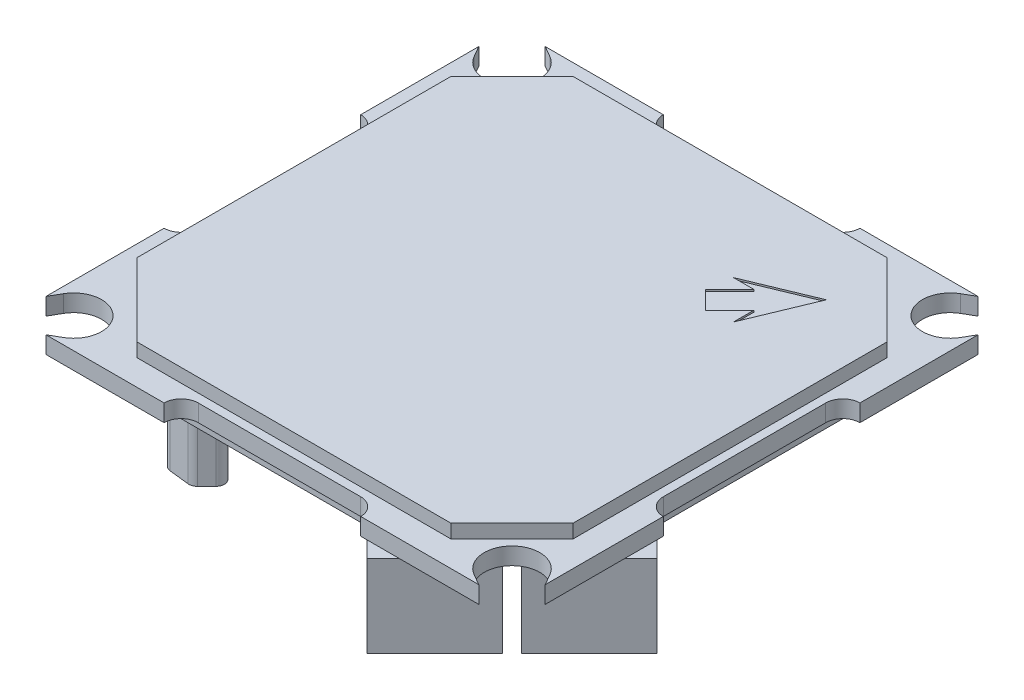
SolidWorks part; units mm, degrees
ref_plane "Front Plane" through (0, 0, 0) normal (0, 0, 1) x (1, 0, 0)
ref_plane "Top Plane" through (0, 0, 0) normal (0, 1, 0) x (1, 0, 0)
ref_plane "Right Plane" through (0, 0, 0) normal (1, 0, 0) x (0, 0, -1)
sketch "Sketch1" plane through (0, 0, 0) normal (0, 1, 0) x (1, 0, 0)
  line L1 (-14.6, -14.6) -> (14.6, -14.6)
  line L2 (-14.6, -14.6) -> (-14.6, 14.6)
  line L3 (-14.6, 14.6) -> (14.6, 14.6)
  line L4 (14.6, -14.6) -> (14.6, 14.6)
  line L5 (-14.6, -14.6) -> (14.6, 14.6) construction
  line L6 (-14.6, 14.6) -> (14.6, -14.6) construction
  point P0 (0, 0)
  dimension "D1" = 29.2
extrude "Boss-Extrude1" add sketch "Sketch1" along normal mid plane 1
sketch "Sketch2" plane through (0, 0.5, 0) normal (0, 1, 0) x (1, 0, 0)
  line L0 (-14.6, 4.75) -> (-14.6, -4.75) construction
  line L1 (-14.6, 14.6) -> (-14.6, -14.6) construction
  line L2 (-13.6, 4.75) -> (-13.6, -4.75)
  line L3 (-15.6, 4.75) -> (-15.6, -4.75)
  arc A0 (-13.6, 4.75) -> (-15.6, 4.75) centre (-14.6, 4.75) ccw
  arc A1 (-15.6, -4.75) -> (-13.6, -4.75) centre (-14.6, -4.75) ccw
  point P4 (-14.6, 0)
  dimension "D1" = 1
  dimension "D2" = 9.5
extrude "Cut-Extrude1" cut sketch "Sketch2" against normal through all both and the other way through all
sketch "Sketch3" plane through (0, 0, 0) normal (1, 0, 0) x (0, 0, -1)
  line L0 (0, 0) -> (0, 0.5) construction
  line L1 (-14.6, 0.5) -> (14.6, 0.5) construction
sketch "Sketch6" plane through (0, 0.5, 0) normal (0, 1, 0) x (1, 0, 0)
  line L4 (19.9404, 1.9799) -> (-1.9799, -19.9404)
  line L6 (19.9404, 1.9799) -> (1.9799, 19.9404)
  line L7 (-1.9799, -19.9404) -> (-19.9404, -1.9799)
  line L8 (1.9799, 19.9404) -> (-19.9404, -1.9799)
  line L9 (8.9803, -8.9803) -> (0, 0) construction
  line L10 (0, 0) -> (-10.9602, -10.9602) construction
  dimension "D1" = 25.4
  dimension "D2" = 31
extrude "Boss-Extrude3" add sketch "Sketch6" along normal blind 0.8
sketch "Sketch4" plane through (0, 0, 0) normal (0, 1, 0) x (1, 0, 0)
  line L0 (-14.2236, 12.0038) -> (-14.6, 12.6558)
  line L1 (12.8163, 12.8163) -> (-12.8163, 12.8163) construction
  line L2 (12.8163, 12.8163) -> (12.8163, -12.8163) construction
  line L3 (12.8163, -12.8163) -> (-12.8163, -12.8163) construction
  line L4 (-12.8163, 12.8163) -> (-12.8163, -12.8163) construction
  line L5 (12.8163, 12.8163) -> (-12.8163, -12.8163) construction
  line L6 (12.8163, -12.8163) -> (-12.8163, 12.8163) construction
  line L7 (-14.6, 14.6) -> (-14.6, 5.75) construction
  line L8 (-14.6, 12.6558) -> (-14.6, 14.6)
  line L9 (-14.6, 14.6) -> (-12.6558, 14.6)
  line L10 (-3.3605, 14.6) -> (-14.6, 14.6) construction
  line L11 (-12.6558, 14.6) -> (-12.0038, 14.2236)
  arc A1 (-14.2236, 12.0038) -> (-12.0038, 14.2236) centre (-12.8163, 12.8163) ccw
  circle A3 centre (12.8163, -12.8163) radius 1.625 construction
  arc A4 (-12.0038, 14.2236) -> (-14.2236, 12.0038) centre (-12.8163, 12.8163) ccw construction
  point P2 (0, 0)
  point P10 (-11.6673, 11.6673)
  point P11 (11.6673, -11.6673)
  dimension "D1" = 3.25
  dimension "D2" = 33
  dimension "D3" = 30
extrude "Cut-Extrude4" cut sketch "Sketch4" along normal through all both and the other way through all contours L0 A1 L11 L9 L8
sketch "Sketch10" plane through (0, 1.3, 0) normal (0, 1, 0) x (1, 0, 0)
  line L0 (13.1, -13.1) -> (13.1, 13.1)
  line L1 (13.1, -13.1) -> (-13.1, -13.1)
  line L2 (13.1, 13.1) -> (-13.1, 13.1)
  line L3 (-13.1, -13.1) -> (-13.1, 13.1)
  line L4 (13.1, -13.1) -> (-13.1, 13.1) construction
  line L5 (14.6, 14.6) -> (-14.6, -14.6) construction
  line L7 (-13.6, 4.75) -> (-13.6, 4.3605) construction
  point P8 (0, 0)
  point P12 (-13.6, 4.5553)
  dimension "D1" = 0.5
extrude "Cut-Extrude9" cut sketch "Sketch10" against normal blind 0.8 flip side to cut
pattern_circular "CirPattern1" count 4 over 360 about axis through (0, 0, 0) along (0, 1, 0) of "Cut-Extrude1", "Cut-Extrude4"
mirror "Mirror3" about plane through (0, 0, 0) normal (0, 1, 0) of "Boss-Extrude3", "Cut-Extrude9"
sketch "Sketch5" plane through (0, -0.5, 0) normal (0, -1, 0) x (1, 0, 0)
  line L0 (4.773, 13.2583) -> (8.7328, 9.2985)
  line L1 (4.773, 13.2583) -> (7.0711, 15.5563)
  line L2 (8.7328, 9.2985) -> (11.0309, 11.5966)
  line L3 (7.0711, 15.5563) -> (11.0309, 11.5966)
  line L4 (9.2985, 8.7328) -> (13.2583, 4.773)
  line L5 (9.2985, 8.7328) -> (11.5966, 11.0309)
  line L6 (13.2583, 4.773) -> (15.5563, 7.0711)
  line L7 (11.5966, 11.0309) -> (15.5563, 7.0711)
  line L8 (12.8163, 12.8163) -> (-12.8163, -12.8163) construction
  line L9 (11.0309, 11.5966) -> (9.2985, 8.7328) construction
  point P12 (10.1647, 10.1647)
  dimension "D1" = 3.25
  dimension "D2" = 12
  dimension "D3" = 0.8
  dimension "D4" = 16
extrude "Boss-Extrude2" add sketch "Sketch5" along normal blind 4.8
ref_plane "Plane1" through (0, 0, 0) normal (0.7071, 0, 0.7071) x (0.7071, 0, -0.7071)
mirror "Mirror1" about plane through (0, 0, 0) normal (0.7071, 0, 0.7071) of "Boss-Extrude2"
sketch "Sketch11" plane through (0, 0.5, 0) normal (0, 1, 0) x (1, 0, 0)
  line L0 (-4.8605, 13.1) -> (-9.5274, 13.1)
  line L1 (-9.5274, 13.1) -> (-13.1, 9.5274)
  line L2 (-13.1, 9.5274) -> (-13.1, 4.8605)
  line L3 (-13.1, 4.8605) -> (-4.8605, 13.1)
  line L4 (-7.0711, 15.5563) -> (-8.0274, 14.6) construction
extrude "Boss-Extrude4" add sketch "Sketch11" along normal up to surface (0.8 mm away) up to face at (0, 1.3, 0)
mirror "Mirror4" about plane through (0, 0, 0) normal (0.7071, 0, 0.7071) of "Boss-Extrude4"
sketch "Sketch12" plane through (0, 1.3, 0) normal (0, 1, 0) x (1, 0, 0)
  line L0 (9.1924, 9.1924) -> (5.3514, 7.6014)
  line L1 (5.3514, 7.6014) -> (6.5407, 7.6014)
  line L2 (6.5407, 7.6014) -> (5.1265, 6.1872)
  line L3 (5.1265, 6.1872) -> (6.1872, 5.1265)
  line L4 (6.1872, 5.1265) -> (7.6014, 6.5407)
  line L5 (7.6014, 6.5407) -> (7.6014, 5.3514)
  line L6 (7.6014, 5.3514) -> (9.1924, 9.1924)
  line L7 (12.8163, 12.8163) -> (-12.8163, -12.8163) construction
  point P11 (5.6569, 5.6569)
  dimension "D1" = 45
  dimension "D2" = 1.5
  dimension "D3" = 5
  dimension "D4" = 8
  dimension "D5" = 2
extrude "Cut-Extrude10" cut sketch "Sketch12" against normal blind 0.1
sketch "Sketch13" plane through (0, -0.5, 0) normal (0, -1, 0) x (1, 0, 0)
  line L0 (-5.6569, 10.9602) -> (-10.9602, 5.6569)
  line L1 (-10.9602, 5.6569) -> (-12.0208, 6.7175)
  line L2 (-12.0208, 6.7175) -> (-11.844, 8.3085)
  line L3 (-11.844, 8.3085) -> (-8.3085, 11.844)
  line L4 (-8.3085, 11.844) -> (-6.7175, 12.0208)
  line L5 (-6.7175, 12.0208) -> (-5.6569, 10.9602)
  line L6 (-12.8163, 12.8163) -> (0, 0) construction
  line L7 (-13.1, 8.8203) -> (-8.8203, 13.1) construction
  point P5 (-8.3085, 8.3085)
  point P11 (-10.0763, 10.0763)
  dimension "D1" = 2.5
  dimension "D2" = 7.5
  dimension "D3" = 5
  dimension "D4" = 11.75
  dimension "D5" = 1.5
extrude "Boss-Extrude5" add sketch "Sketch13" along normal blind 5
fillet "Fillet1" radius 0.5 6 edges at (-5.6569, -3.4, 10.9602) (-6.7175, -3.4, 12.0208) (-8.3085, -3.4, 11.844) (-11.844, -3.4, 8.3085) (-12.0208, -3.4, 6.7175) (-10.9602, -3.4, 5.6569)
sketch "Sketch14" plane through (0, -0.5, 0) normal (0, -1, 0) x (1, 0, 0)
  line L0 (-14.6, 5.75) -> (-14.6, 12.6558) construction
  line L1 (-12.6558, 14.6) -> (-5.75, 14.6) construction
  circle A0 centre (-12.6, 2.6) radius 0.675
  circle A1 centre (-12.6, 4.6) radius 0.675
  dimension "D1" = 1.35
  dimension "D2" = 2
  dimension "D3" = 2
  dimension "D4" = 10
extrude "Boss-Extrude7" add sketch "Sketch14" along normal blind 5
